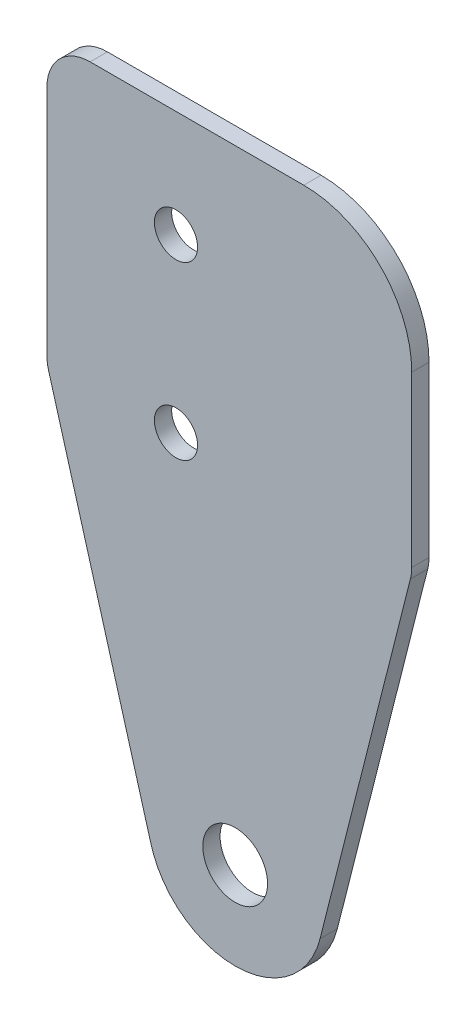
SolidWorks part; units mm, degrees
ref_plane "Front Plane" through (0, 0, 0) normal (0, 0, 1) x (1, 0, 0)
ref_plane "Top Plane" through (0, 0, 0) normal (0, 1, 0) x (1, 0, 0)
ref_plane "Right Plane" through (0, 0, 0) normal (1, 0, 0) x (0, 0, -1)
sketch "Sketch1" plane through (0, 0, 0) normal (0, 0, 1) x (1, 0, 0)
  line L0 (36.798, 101.1427) -> (103.7813, 99.6461) construction
  line L1 (271.4901, 97.177) -> (276.1996, 80.6752)
  line L2 (273.4133, 110.5288) -> (283.3061, 110.5288)
  line L3 (271.4133, 108.5288) -> (271.4133, 97.7259)
  line L4 (271.4133, 97.4461) -> (288.3061, 97.4461) construction
  line L5 (288.3061, 105.5288) -> (288.3061, 97.6954)
  line L6 (288.2448, 97.2044) -> (284.0598, 80.6805)
  arc A0 (284.0598, 80.6805) -> (276.1996, 80.6752) centre (280.129, 81.676) cw
  circle A1 centre (280.129, 81.676) radius 1.5
  arc A2 (288.3061, 105.5288) -> (283.3061, 110.5288) centre (283.3061, 105.5288) ccw
  arc A3 (273.4133, 110.5288) -> (271.4133, 108.5288) centre (273.4133, 108.5288) ccw
  arc A4 (288.2448, 97.2044) -> (288.3061, 97.6954) centre (286.3061, 97.6954) ccw
  arc A5 (271.4901, 97.177) -> (271.4133, 97.7259) centre (273.4133, 97.7259) cw
  circle A6 centre (277.3874, 105.5814) radius 1
  circle A7 centre (277.3874, 97.639) radius 1
  dimension "D2" = 5
  dimension "D3" = 2
  dimension "D4" = 2
  dimension "D1" = 67
extrude "Boss-Extrude1" add sketch "Sketch1" along normal blind 0.8
